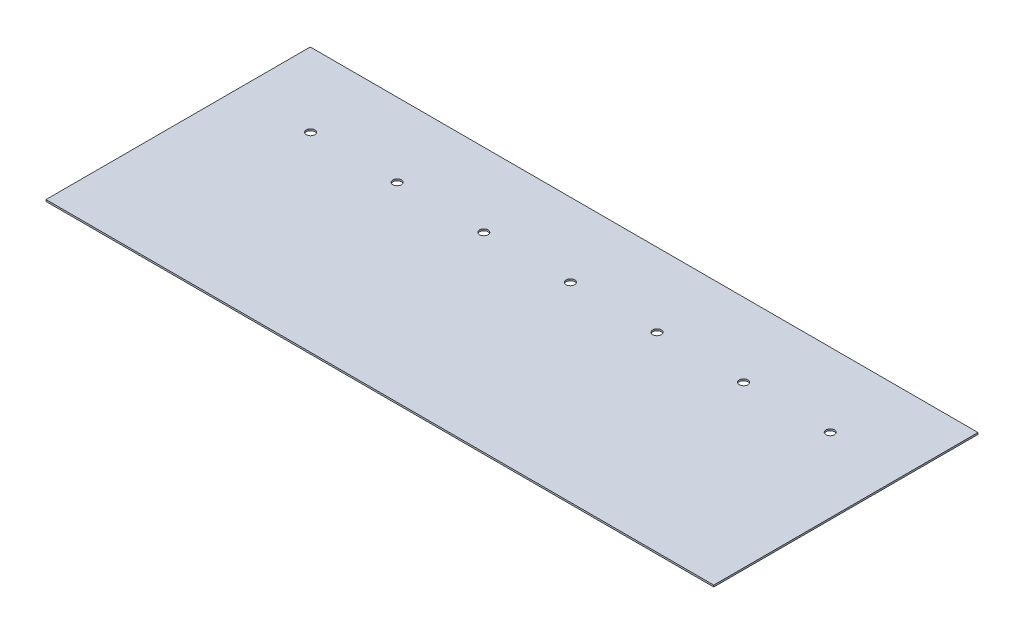
SolidWorks part; units mm, degrees
ref_plane "Front Plane" through (0, 0, 0) normal (0, 0, 1) x (1, 0, 0)
ref_plane "Top Plane" through (0, 0, 0) normal (0, 1, 0) x (1, 0, 0)
ref_plane "Right Plane" through (0, 0, 0) normal (1, 0, 0) x (0, 0, -1)
sketch "Sketch1" plane through (0, 0, 0) normal (0, 1, 0) x (1, 0, 0)
  line L0 (195.834, -199.9996) -> (195.834, -88.2396) construction
  line L1 (0, 0) -> (391.668, 0)
  line L2 (0, 0) -> (0, -199.9996)
  line L3 (0, -199.9996) -> (391.668, -199.9996)
  line L4 (391.668, 0) -> (391.668, -199.9996)
  line L5 (195.834, -88.2396) -> (391.668, -88.2396) construction
  line L6 (195.834, -88.2396) -> (0, -88.2396) construction
  circle A0 centre (195.834, -88.2396) radius 2.5
  circle A1 centre (145.034, -88.2396) radius 2.5
  circle A2 centre (94.234, -88.2396) radius 2.5
  circle A3 centre (43.434, -88.2396) radius 2.5
  circle A4 centre (195.834, -88.2396) radius 2.5
  circle A5 centre (145.034, -88.2396) radius 2.5
  circle A6 centre (94.234, -88.2396) radius 2.5
  circle A7 centre (246.634, -88.2396) radius 2.5
  circle A8 centre (195.834, -88.2396) radius 2.5
  circle A9 centre (145.034, -88.2396) radius 2.5
  circle A10 centre (297.434, -88.2396) radius 2.5
  circle A11 centre (246.634, -88.2396) radius 2.5
  circle A12 centre (195.834, -88.2396) radius 2.5
  circle A13 centre (246.634, -88.2396) radius 2.5
  circle A14 centre (297.434, -88.2396) radius 2.5
  circle A15 centre (348.234, -88.2396) radius 2.5
  dimension "D4" = 5
  dimension "D1" = 199.9996
  dimension "D2" = 391.668
  dimension "D3" = 111.76
  dimension "D5" = 4
  dimension "D6" = 4
extrude "Boss-Extrude1" add sketch "Sketch1" against normal blind 1 contours L4 L1 L2 L3 A15 A10 A7 A3 A2 A1 A0
ref_plane "Plane1" through (195.834, 0, 0) normal (-1, 0, 0) x (0, 0, 1)
ref_plane "Plane2" through (0, 0, 99.9998) normal (0, 0, -1) x (-1, 0, 0)
ref_plane "Plane3" through (0, 0, 88.2396) normal (0, 0, -1) x (-1, 0, 0)
sketch "Sketch2" plane through (0, 0, 0) normal (0, 1, 0) x (1, 0, 0)
  line L0 (0, 0) -> (0, -45)
  line L1 (0, 0) -> (0, -199.9996) construction
  line L2 (0, -45) -> (391.668, -45)
  line L3 (391.668, 0) -> (391.668, -199.9996) construction
  line L4 (0, 0) -> (391.668, 0)
  line L5 (391.668, 0) -> (391.668, -45)
  dimension "D1" = 45
extrude "Cut-Extrude1" cut sketch "Sketch2" against normal through all both and the other way through all
